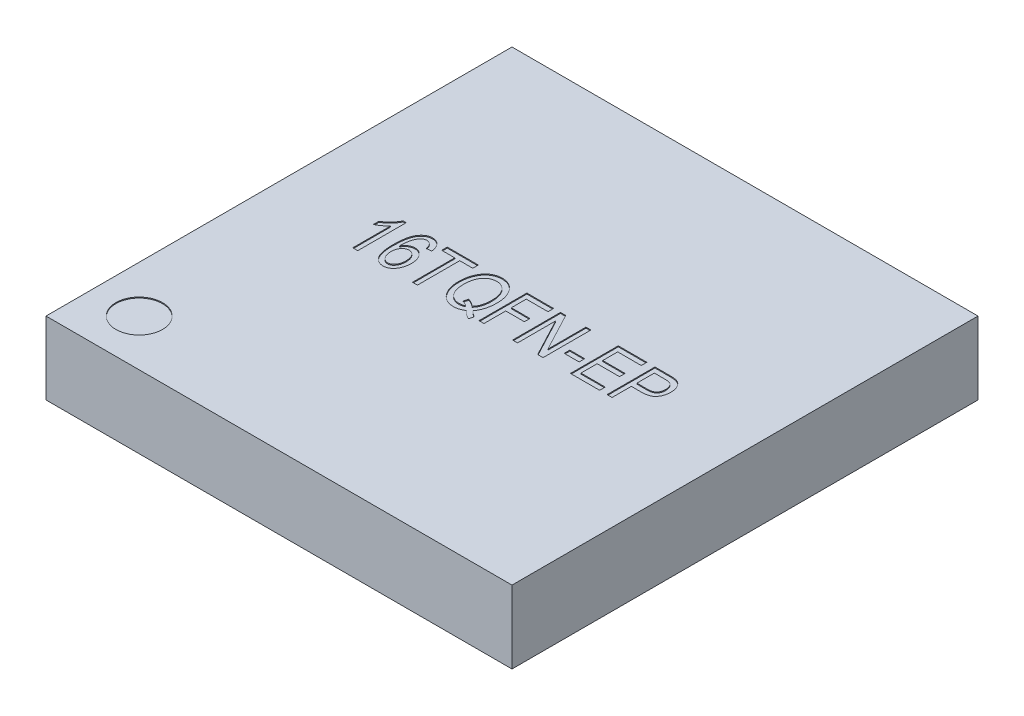
SolidWorks part; units mm, degrees
ref_plane "Front Plane" through (0, 0, 0) normal (0, 0, 1) x (1, 0, 0)
ref_plane "Top Plane" through (0, 0, 0) normal (0, 1, 0) x (1, 0, 0)
ref_plane "Right Plane" through (0, 0, 0) normal (1, 0, 0) x (0, 0, -1)
sketch "Sketch1" plane through (0, 0, 0) normal (0, 1, 0) x (1, 0, 0)
  line L1 (-2.5, -2.5) -> (2.5, -2.5)
  line L2 (-2.5, -2.5) -> (-2.5, 2.5)
  line L3 (-2.5, 2.5) -> (2.5, 2.5)
  line L4 (2.5, -2.5) -> (2.5, 2.5)
  line L5 (-2.5, -2.5) -> (2.5, 2.5) construction
  line L6 (-2.5, 2.5) -> (2.5, -2.5) construction
  point P0 (0, 0)
  dimension "D1" = 5
extrude "Boss-Extrude1" add sketch "Sketch1" along normal blind 0.78
sketch "Sketch2" plane through (0, 0.78, 0) normal (0, 1, 0) x (1, 0, 0)
  line L0 (-2.5, 2.5) -> (-2.5, -2.5) construction
  line L1 (-2.5, -2.5) -> (2.5, -2.5) construction
  circle A0 centre (-2, -2) radius 0.25
  dimension "D3" = 0.5
  dimension "D1" = 0.5
  dimension "D2" = 0.5
extrude "Cut-Extrude1" cut sketch "Sketch2" against normal blind 0.01
sketch "Sketch3" plane through (0, 0.78, 0) normal (0, 1, 0) x (1, 0, 0)
  line L0 (-1.655, -0.22) -> (1.6525, -0.22) construction
  text T0 "16TQFN-EP" font "Arial Narrow" height in points 2
  point P3 (-1.4132, -0.2249)
  point P4 (-1.655, -0.22)
extrude "Cut-Extrude2" cut sketch "Sketch3" against normal blind 0.01
